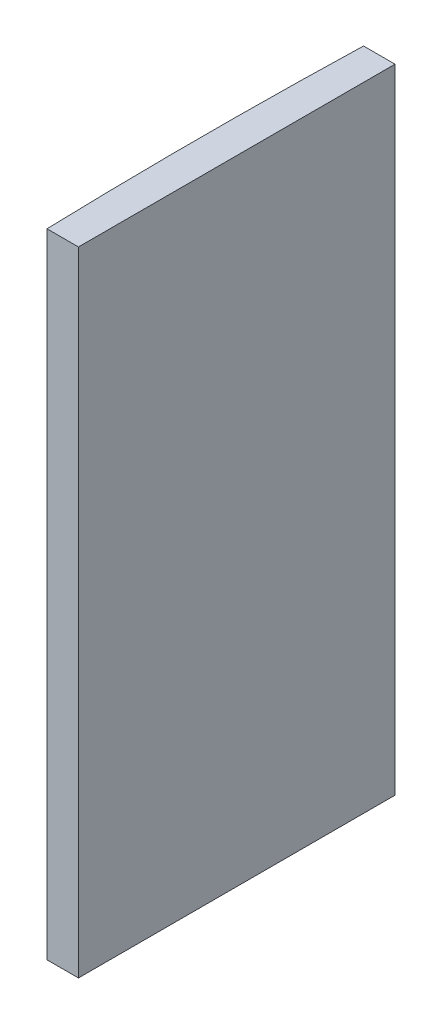
SolidWorks part; units mm, degrees
ref_plane "前视基准面" through (0, 0, 0) normal (0, 0, 1) x (1, 0, 0)
ref_plane "上视基准面" through (0, 0, 0) normal (0, 1, 0) x (1, 0, 0)
ref_plane "右视基准面" through (0, 0, 0) normal (1, 0, 0) x (0, 0, -1)
sketch "草图1" plane through (0, 0, 0) normal (0, 1, 0) x (1, 0, 0)
  line L0 (10.7432, 0) -> (-607.0701, 0) construction
  line L1 (-512.2271, 15) -> (-509.2448, 15)
  line L2 (-512.2271, -15) -> (-509.2448, -15)
  line L3 (-509.2448, 15) -> (-509.2448, -15)
  arc A0 (-512.2271, 15) -> (-512.2271, -15) centre (4.3552, 0) ccw
  point P19 (-512.4448, 0)
  point P20 (-509.2448, 0)
  dimension "D2" = 15
  dimension "D3" = 516.8
  dimension "D4" = 3.2
  dimension "D1" = 15
extrude "凸台-拉伸1" add sketch "草图1" along normal blind 60
